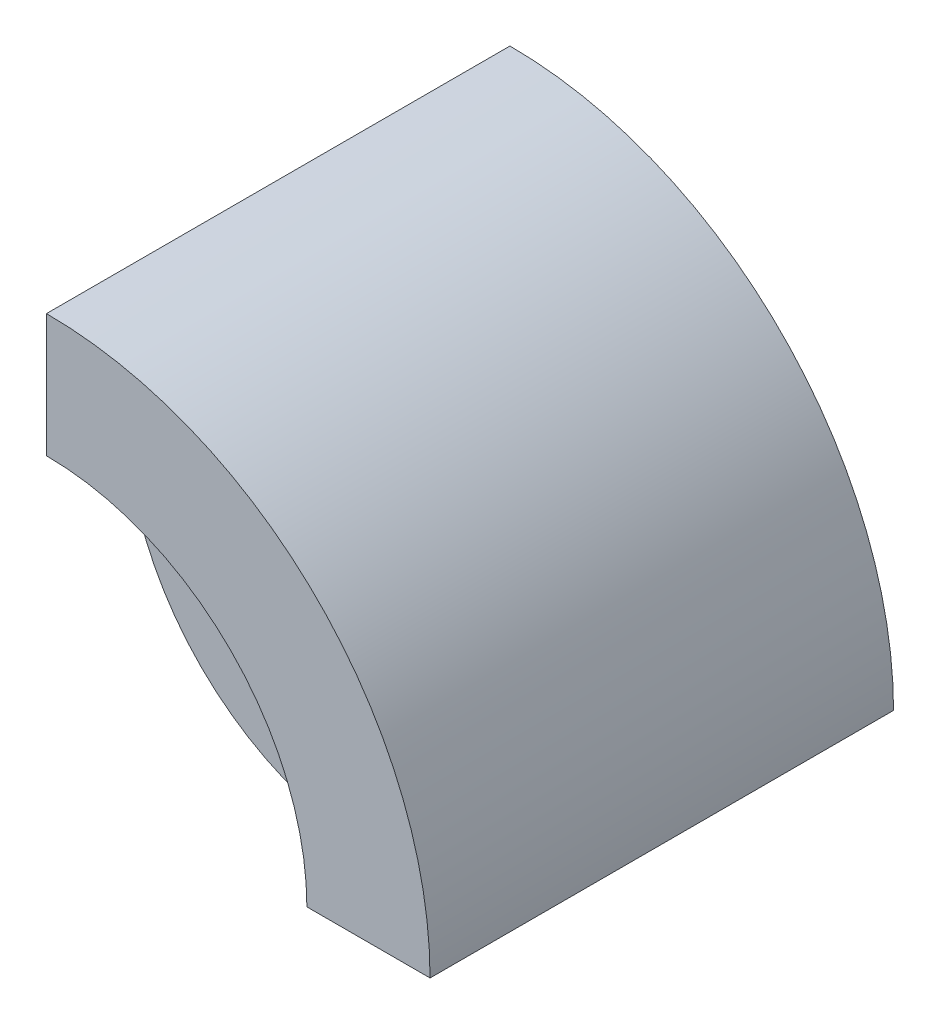
SolidWorks part; units mm, degrees
ref_plane "Front Plane" through (0, 0, 0) normal (0, 0, 1) x (1, 0, 0)
ref_plane "Top Plane" through (0, 0, 0) normal (0, 1, 0) x (1, 0, 0)
ref_plane "Right Plane" through (0, 0, 0) normal (1, 0, 0) x (0, 0, -1)
sketch "Sketch1" plane through (0, 0, 0) normal (0, 0, 1) x (1, 0, 0)
  line L0 (0, 28.575) -> (0, 19.0514)
  line L1 (28.575, 0) -> (19.0514, 0)
  line L2 (0, 0) -> (18.0981, 18.0981) construction
  line L3 (13.4704, 13.4704) -> (13.4714, 13.4714)
  circle A0 centre (0, 0) radius 19.0514
  circle A1 centre (0, 0) radius 11.1
  arc A2 (28.575, 0) -> (0, 28.575) centre (0, 0) ccw
  spline S0 degree 2 poles (0, 28.575) (21.9087, 21.9087) (28.575, 0) knots 0 0 0 1 1 1 construction
  point P13 (0, 0)
  dimension "D2" = 22.2
extrude "Boss-Extrude5" add sketch "Sketch1" along normal blind 9.525
sketch "Sketch2" plane through (0, 0, 0) normal (0, 0, -1) x (-1, 0, 0)
  line L0 (0, 28.575) -> (0, 19.0514) construction
  line L1 (-28.575, 0) -> (-19.0514, 0) construction
  line L2 (0, 28.575) -> (0, 19.4)
  line L3 (-28.575, 0) -> (-19.4, 0)
  arc A0 (0, 19.4) -> (-19.4, 0) centre (0, 0) ccw
  parabola Q1 (0, 28.575) -> (-28.575, 0) focus (-4.7056, 4.7056) apex (-18.0981, 18.0981)
extrude "Right Side" [suppressed] add sketch "Sketch2" along normal blind 9.525
sketch "Sketch3" plane through (0, 0, 9.525) normal (0, 0, 1) x (1, 0, 0)
  line L2 (0, 28.575) -> (0, 19.4)
  line L3 (19.4, 0) -> (28.575, 0)
  line L4 (0, 28.575) -> (0, 19.4)
  line L5 (19.4, 0) -> (28.575, 0)
  arc A1 (19.4, 0) -> (0, 19.4) centre (0, 0) ccw
  arc A2 (19.4, 0) -> (0, 19.4) centre (0, 0) ccw
  parabola Q1 (28.575, 0) -> (0, 28.575) focus (4.7056, 4.7056) apex (18.0981, 18.0981)
  parabola Q2 (28.575, 0) -> (0, 28.575) focus (4.7056, 4.7056) apex (18.0981, 18.0981) construction
  arc M10 (28.575, 0) -> (0, 28.575) centre (0, 0) ccw
  dimension "D1" = 0
extrude "Left Side" add sketch "Sketch3" along normal blind 25 contours Q2 M10
sketch "Sketch7" [suppressed] plane through (0, 0, 0) normal (0, 0, -1) x (-1, 0, 0)
  line L1 (-28.575, 0) -> (-11.647, 0)
  line L2 (-28.575, 0) -> (-28.575, 5.4458)
  line L3 (-28.575, 5.4458) -> (-11.647, 5.4458)
  line L4 (-11.647, 0) -> (-11.647, 5.4458)
